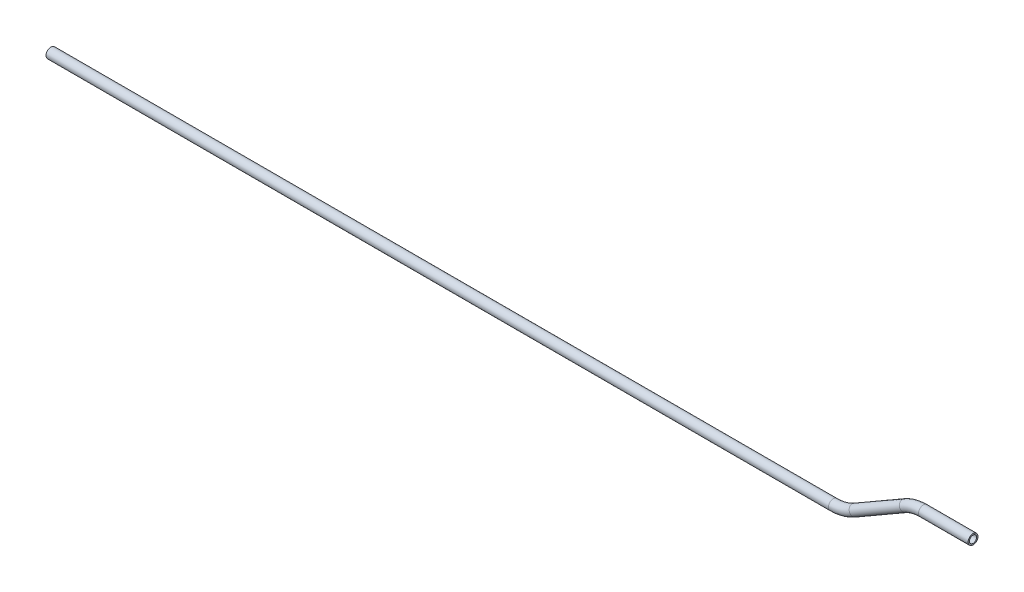
SolidWorks part; units mm, degrees
material "AISI 316 Stainless Steel Sheet (SS)"
ref_plane "Front Plane" through (0, 0, 0) normal (0, 0, 1) x (1, 0, 0)
ref_plane "Top Plane" through (0, 0, 0) normal (0, 1, 0) x (1, 0, 0)
ref_plane "Right Plane" through (0, 0, 0) normal (1, 0, 0) x (0, 0, -1)
sketch "Sketch1" plane through (0, 0, 0) normal (0, 0, 1) x (1, 0, 0)
  line L0 (0, 0) -> (31.76, 0)
  line L1 (-11.8306, -3.17) -> (-43.9793, -21.731)
  line L2 (-57.672, -25.4) -> (-558.3341, -25.4)
  line L3 (31.76, 0) -> (-16.7409, 0) construction
  line L4 (-558.3341, -25.4) -> (-502.4016, -25.4) construction
  line L5 (4.6446, 6.342) -> (-46.7361, -23.3227) construction
  arc A0 (0, 0) -> (-11.8306, -3.17) centre (0, -23.6612) ccw
  arc A1 (-43.9793, -21.731) -> (-57.672, -25.4) centre (-57.672, 1.9855) cw
  point P8 (-50.3341, -25.4)
  point P14 (-6.34, 0)
  dimension "D1" = 30
  dimension "D2" = 30
  dimension "D3" = 38.1
  dimension "D4" = 50.8
  dimension "D5" = 508
ref_plane "Plane1" through (31.76, 0, 0) normal (1, 0, 0) x (0, 0, -1)
sketch "Sketch2" plane through (31.76, 0, 0) normal (1, 0, 0) x (0, 0, -1)
  circle A0 centre (0, 0) radius 3.175
  circle A1 centre (0, 0) radius 2.286
  dimension "D1" = 4.572
  dimension "D2" = 6.35
sweep "Sweep1" add profiles "Sketch2" path "Sketch1"
